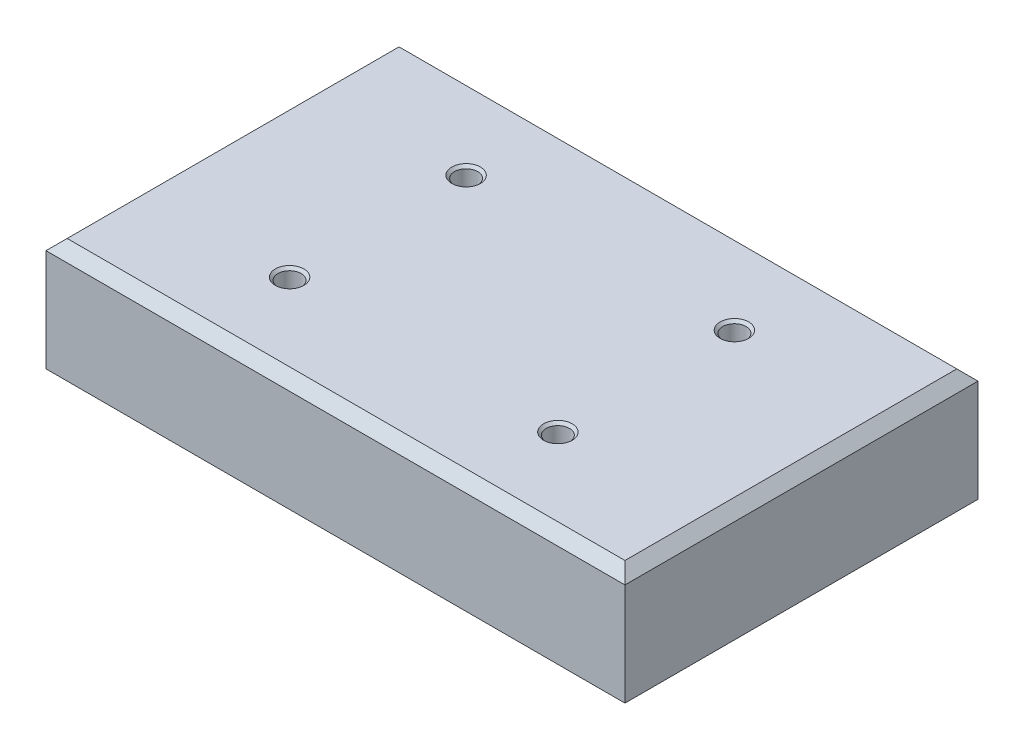
SolidWorks part; units mm, degrees
ref_plane "Front Plane" through (0, 0, 0) normal (0, 0, 1) x (1, 0, 0)
ref_plane "Top Plane" through (0, 0, 0) normal (0, 1, 0) x (1, 0, 0)
ref_plane "Right Plane" through (0, 0, 0) normal (1, 0, 0) x (0, 0, -1)
sketch "Эскиз1" plane through (0, 0, 0) normal (0, 1, 0) x (1, 0, 0)
  line L0 (0, 0) -> (82, 0)
  line L1 (0, 0) -> (0, 50)
  line L2 (82, 0) -> (82, 50)
  line L3 (0, 50) -> (82, 50)
  dimension "D1" = 82
  dimension "D2" = 50
extrude "Бобышка-Вытянуть1" add sketch "Эскиз1" along normal blind 16
chamfer "Фаска1" distance 1.5 angle 45 4 edges at (0, 16, -25) (41, 16, -50) (41, 16, 0) (82, 16, -25)
sketch "Эскиз2" plane through (0, 16, 0) normal (0, 1, 0) x (1, 0, 0)
  line L0 (1.5, 25) -> (80.5, 25) construction
  line L1 (1.5, 48.5) -> (1.5, 1.5) construction
  line L2 (80.5, 1.5) -> (80.5, 48.5) construction
  line L3 (41, 48.5) -> (41, 1.5) construction
  line L4 (80.5, 48.5) -> (1.5, 48.5) construction
  line L5 (1.5, 1.5) -> (80.5, 1.5) construction
  line L6 (60, 37.5) -> (60, 12.5) construction
  line L7 (22, 37.5) -> (60, 37.5) construction
  line L8 (22, 37.5) -> (22, 12.5) construction
  line L9 (22, 12.5) -> (60, 12.5) construction
  circle A0 centre (22, 37.5) radius 2
  circle A1 centre (22, 12.5) radius 2
  circle A2 centre (60, 12.5) radius 2
  circle A3 centre (60, 37.5) radius 2
  dimension "D1" = 4
  dimension "D2" = 25
  dimension "D3" = 12.5
  dimension "D4" = 38
  dimension "D5" = 38
hole_wizard "Отверстие обработанное метчиком M41" positions "Трехмерный эскиз1" profile "Эскиз3" tap size "M4" standard "DIN"
sketch3d "Трехмерный эскиз1"
  point P0 (22, 16, -37.5)
  point P3 (22, 16, -12.5)
  point P6 (60, 16, -37.5)
  point P9 (60, 16, -12.5)
sketch "Эскиз3" plane through (22, 16, -37.5) normal (1, 0, 0) x (0, 0, 1)
  line L0 (0, 0) -> (0, 8)
  line L1 (0, 8) -> (1.65, 7.0086)
  line L2 (1.65, 7.0086) -> (1.65, 0.375)
  line L3 (1.65, 0.375) -> (2.025, 0)
  line L5 (2.025, 0) -> (0, 0)
  line L6 (-1.65, 0.375) -> (-2.025, 0) construction
  line L10 (0, 8) -> (-1.65, 7.0086) construction
  line L11 (0, -6.35) -> (0, 107.95) construction
  dimension "Диаметр сверла" = 3.3
  dimension "Глубина сверла" = 8
  dimension "Диаметр передней зенковки" = 4.05
  dimension "Угол передней зенковки" = 90
  dimension "Угол заточки сверла" = 118
cosmetic thread "Отверстие резьбы1" parameters "D1"=6, "D2"=4
cosmetic thread "Отверстие резьбы2" parameters "D1"=6, "D2"=4
cosmetic thread "Отверстие резьбы3" parameters "D1"=6, "D2"=4
cosmetic thread "Отверстие резьбы4" parameters "D1"=6, "D2"=4
